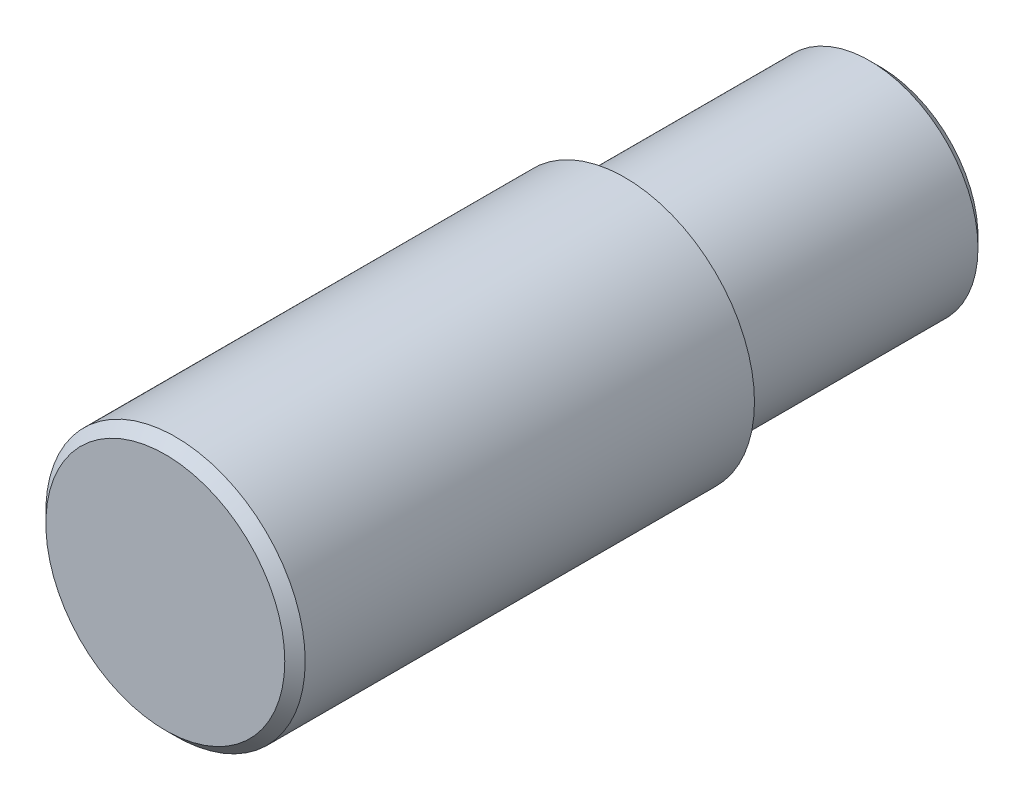
SolidWorks part; units mm, degrees
ref_plane "Front Plane" through (0, 0, 0) normal (0, 0, 1) x (1, 0, 0)
ref_plane "Top Plane" through (0, 0, 0) normal (0, 1, 0) x (1, 0, 0)
ref_plane "Right Plane" through (0, 0, 0) normal (1, 0, 0) x (0, 0, -1)
sketch "Sketch1" plane through (0, 0, 0) normal (0, 0, 1) x (1, 0, 0)
  circle A0 centre (0, 0) radius 12.7
  dimension "D1" = 25.4
extrude "Boss-Extrude1" add sketch "Sketch1" along normal blind 45
cosmetic thread "Cosmetic Thread1" parameters "D1"=44.9999, "D2"=10.619
sketch "Sketch2" plane through (0, 0, 0) normal (0, 0, -1) x (-1, 0, 0)
  circle A0 centre (0, 0) radius 10.59
  dimension "D1" = 21.18
extrude "Boss-Extrude2" add sketch "Sketch2" along normal blind 25
cosmetic thread "Cosmetic Thread2" parameters "D1"=10, "D2"=10.619
fillet "Fillet1" radius 1 1 edges at (-10.59, 0, 0)
chamfer "Chamfer2" distance 1 angle 45 1 edges at (-10.59, 0, -25)
chamfer "Chamfer3" distance 1 angle 45 1 edges at (12.7, 0, 45)
